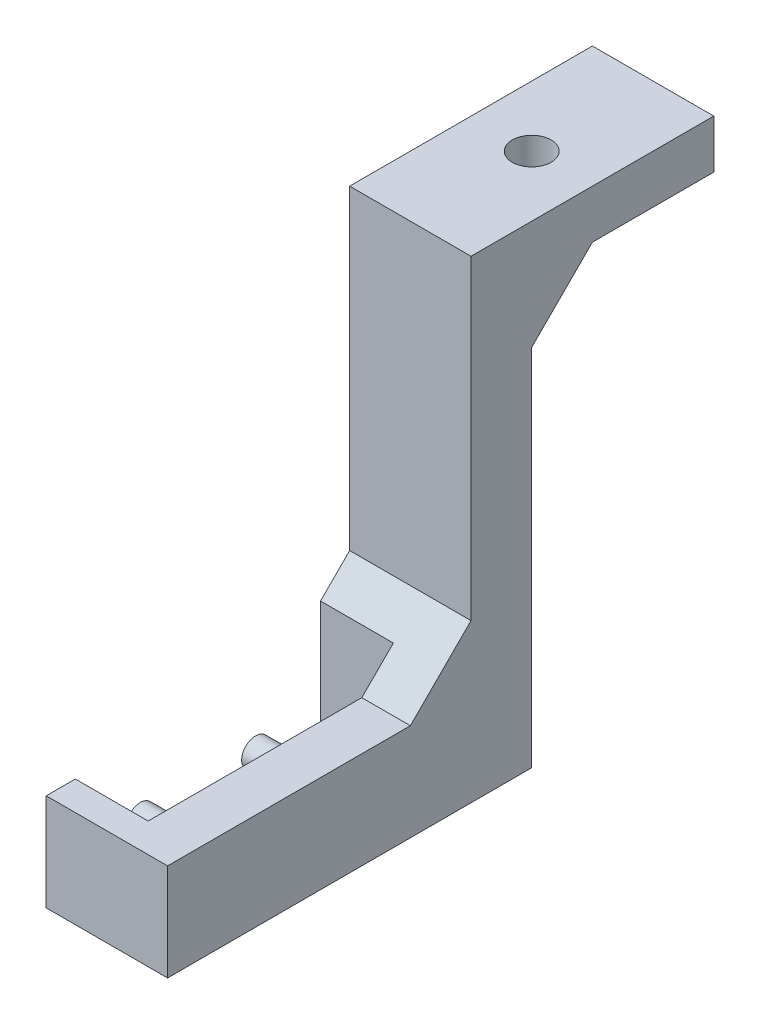
SolidWorks part; units mm, degrees
ref_plane "前视基准面" through (0, 0, 0) normal (0, 0, 1) x (1, 0, 0)
ref_plane "上视基准面" through (0, 0, 0) normal (0, 1, 0) x (1, 0, 0)
ref_plane "右视基准面" through (0, 0, 0) normal (1, 0, 0) x (0, 0, -1)
sketch "草图1" plane through (0, 0, 0) normal (1, 0, 0) x (0, 0, -1)
  line L0 (0, 0) -> (30, 0)
  line L1 (30, 0) -> (30, 35)
  line L2 (30, 35) -> (45, 35)
  line L3 (45, 35) -> (45, 39)
  line L4 (45, 39) -> (25, 39)
  line L5 (25, 39) -> (25, 8)
  line L6 (25, 8) -> (0, 8)
  line L7 (0, 8) -> (0, 0)
  dimension "D1" = 20
  dimension "D2" = 4
  dimension "D3" = 5
  dimension "D4" = 30
  dimension "D5" = 8
  dimension "D6" = 31
extrude "凸台-拉伸1" add sketch "草图1" along normal mid plane 10
sketch "草图2" plane through (-5, 0, 0) normal (-1, 0, 0) x (0, 0, 1)
  line L0 (-25, 8) -> (0, 8) construction
  line L1 (-22.6, 8) -> (-2.4, 8)
  line L2 (-22.6, 8) -> (-22.6, 0)
  line L3 (-22.6, 0) -> (-2.4, 0)
  line L4 (-2.4, 8) -> (-2.4, 0)
  line L5 (0, 8) -> (0, 0) construction
  dimension "D1" = 8
  dimension "D2" = 20.2
  dimension "D3" = 2.4
extrude "切除-拉伸1" cut sketch "草图2" against normal blind 6
sketch "草图3" plane through (1, 0, 0) normal (-1, 0, 0) x (0, 0, 1)
  line L0 (-22.6, 0) -> (-2.4, 0) construction
  line L1 (-17.25, 2.5) -> (-7.75, 2.5) construction
  line L2 (-12.5, 2.5) -> (-12.5, 0) construction
  circle A0 centre (-17.25, 2.5) radius 1.15
  circle A1 centre (-7.75, 2.5) radius 1.15
  dimension "D1" = 2.3
  dimension "D2" = 2.3
  dimension "D3" = 2.5
  dimension "D4" = 2.5
  dimension "D5" = 9.5
extrude "凸台-拉伸2" add sketch "草图3" along normal blind 6
chamfer "倒角1" distance 5 angle 45 2 edges at (0, 8, -25) (0, 35, -30)
sketch "草图4" plane through (0, 35, 0) normal (0, -1, 0) x (1, 0, 0)
  line L0 (5, -45) -> (-5, -45) construction
  circle A0 centre (0, -35) radius 3
  dimension "D1" = 6
  dimension "D2" = 10
extrude "切除-拉伸2" cut sketch "草图4" along normal blind 6
sketch "草图5" plane through (0, 35, 0) normal (0, -1, 0) x (1, 0, 0)
  circle A0 centre (0, -35) radius 1.6
  dimension "D1" = 3.2
extrude "切除-拉伸3" cut sketch "草图5" against normal through all
